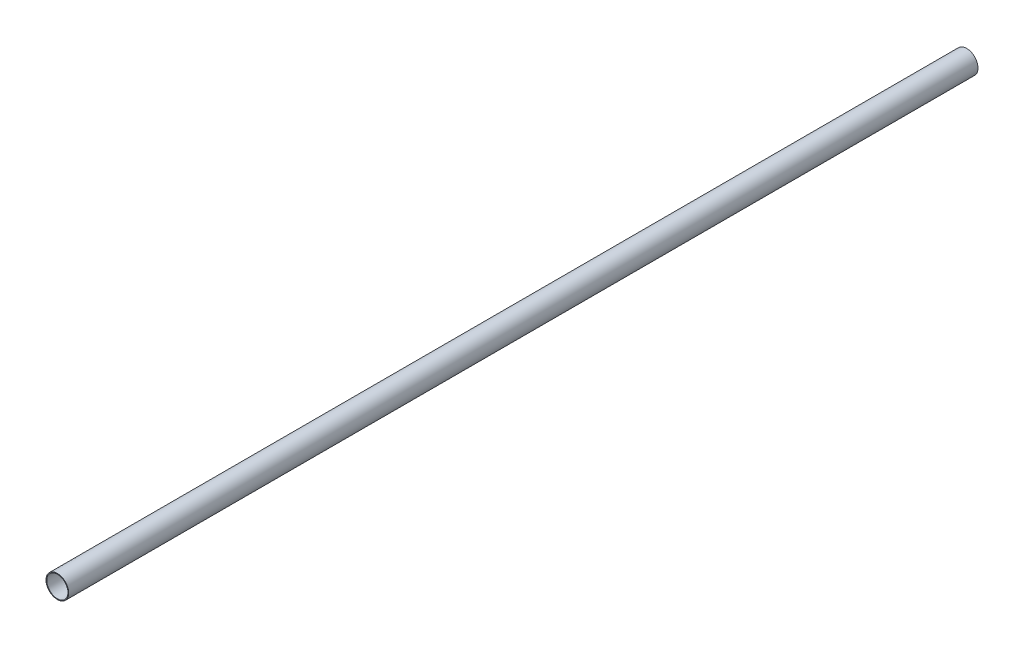
SolidWorks part; units mm, degrees
ref_plane "Front Plane" through (0, 0, 0) normal (0, 0, 1) x (1, 0, 0)
ref_plane "Top Plane" through (0, 0, 0) normal (0, 1, 0) x (1, 0, 0)
ref_plane "Right Plane" through (0, 0, 0) normal (1, 0, 0) x (0, 0, -1)
sketch "Sketch1" plane through (0, 0, 0) normal (0, 0, 1) x (1, 0, 0)
  circle A0 centre (0, 0) radius 15
  circle A1 centre (0, 0) radius 14
  dimension "D1" = 30
  dimension "D2" = 28
extrude "Boss-Extrude1" add sketch "Sketch1" along normal blind 1200
